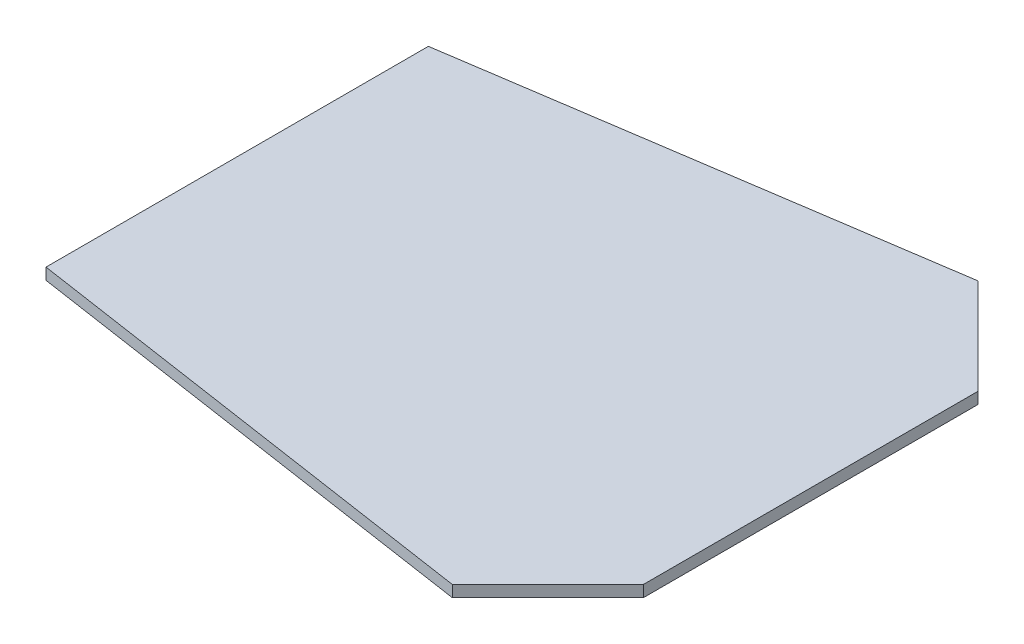
SolidWorks part; units mm, degrees
ref_plane "Front Plane" through (0, 0, 0) normal (0, 0, 1) x (1, 0, 0)
ref_plane "Top Plane" through (0, 0, 0) normal (0, 1, 0) x (1, 0, 0)
ref_plane "Right Plane" through (0, 0, 0) normal (1, 0, 0) x (0, 0, -1)
sketch "Sketch1" plane through (0, 0, 0) normal (0, 1, 0) x (1, 0, 0)
  line L0 (0, 0) -> (0, 400)
  line L1 (0, 400) -> (500, 475)
  line L2 (500, 475) -> (600, 375)
  line L3 (600, 375) -> (600, 25)
  line L4 (600, 25) -> (500, -75)
  line L5 (500, -75) -> (0, 0)
  dimension "D1" = 400
  dimension "D2" = 500
  dimension "D3" = 75
  dimension "D4" = 100
  dimension "D5" = 100
  dimension "D6" = 100
  dimension "D7" = 75
extrude "Boss-Extrude1" add sketch "Sketch1" along normal blind 12
sketch "Sketch2" plane through (0, 12, 0) normal (0, 1, 0) x (1, 0, 0)
  line L0 (600, 200) -> (0, 200) construction
  line L1 (600, 25) -> (600, 375) construction
  line L2 (0, 400) -> (0, 0) construction
